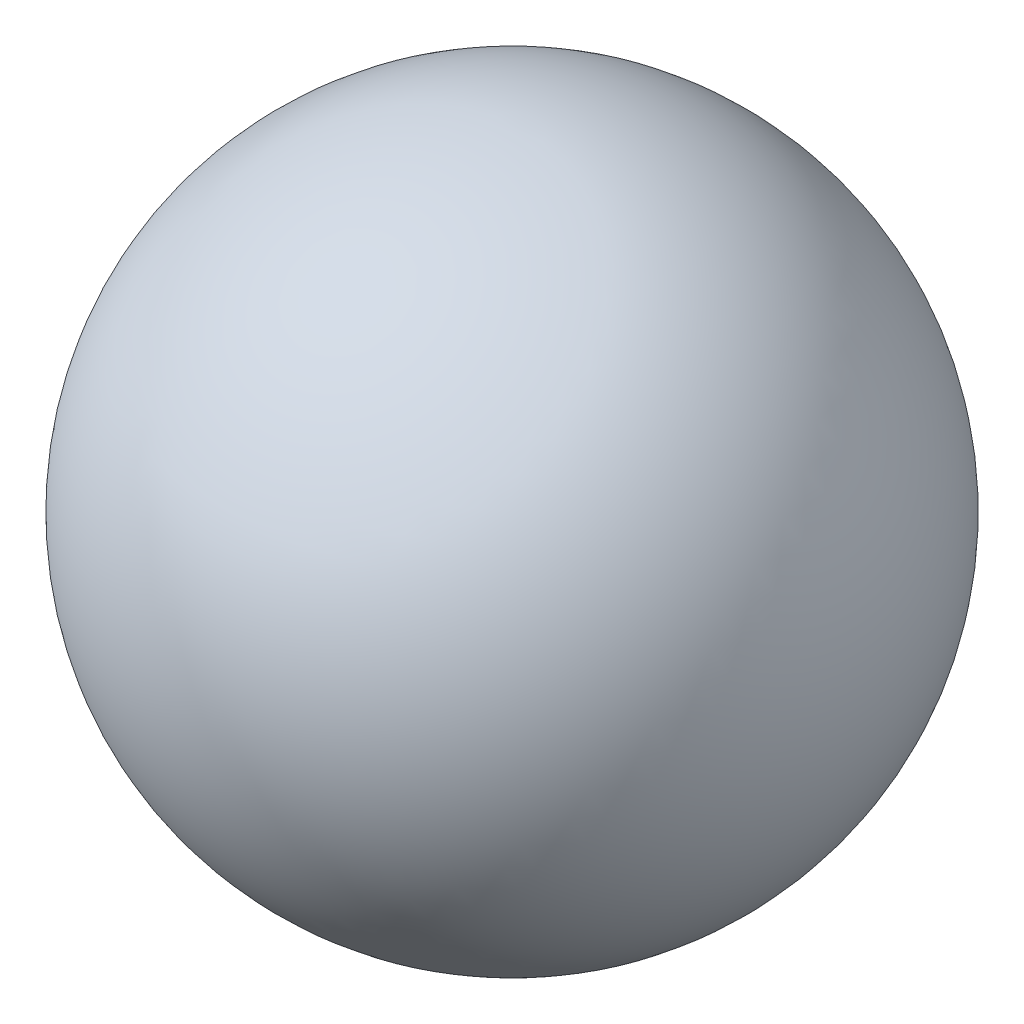
SolidWorks part; units mm, degrees
ref_plane "Front Plane" through (0, 0, 0) normal (0, 0, 1) x (1, 0, 0)
ref_plane "Top Plane" through (0, 0, 0) normal (0, 1, 0) x (1, 0, 0)
ref_plane "Right Plane" through (0, 0, 0) normal (1, 0, 0) x (0, 0, -1)
sketch "Sketch1" plane through (0, 0, 0) normal (0, 0, 1) x (1, 0, 0)
  line L0 (0, 3.575) -> (0, -3.575) construction
  line L1 (0, 3.575) -> (0, -3.575)
  arc A0 (0, 3.575) -> (0, -3.575) centre (0, 0) ccw
  dimension "D1" = 7.15
revolve "Revolve2" add sketch "Sketch1" angle 360 about L0
